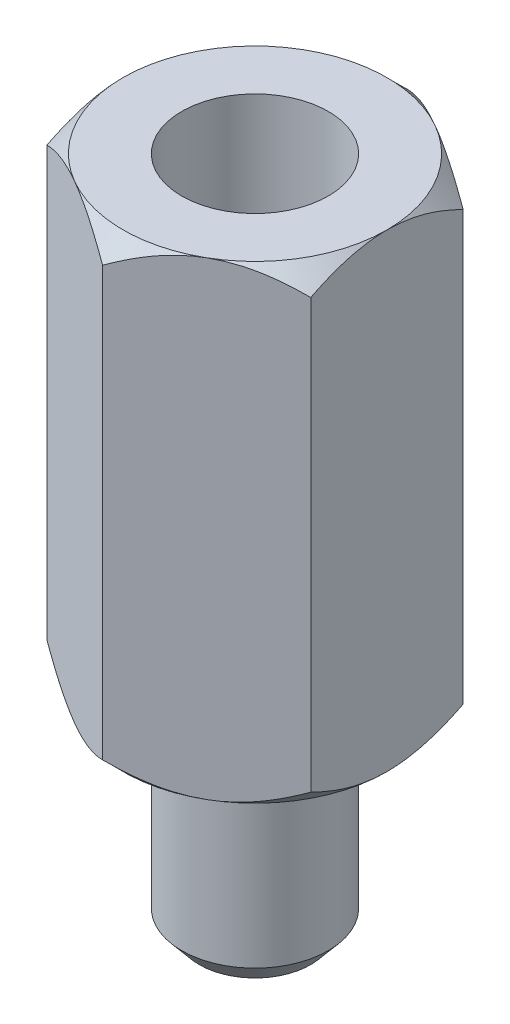
SolidWorks part; units mm, degrees
ref_plane "Front Plane" through (0, 0, 0) normal (0, 0, 1) x (1, 0, 0)
ref_plane "Top Plane" through (0, 0, 0) normal (0, 1, 0) x (1, 0, 0)
ref_plane "Right Plane" through (0, 0, 0) normal (1, 0, 0) x (0, 0, -1)
sketch "Sketch1" plane through (0, 0, 0) normal (0, 1, 0) x (1, 0, 0)
  circle A0 centre (0, 0) radius 1.25
  dimension "D1" = 2.5
extrude "Boss-Extrude1" add sketch "Sketch1" along normal blind 3.5
sketch "Sketch2" plane through (0, 3.5, 0) normal (0, 1, 0) x (1, 0, 0)
  line L1 (2.25, -1.299) -> (2.25, 1.299)
  line L2 (2.25, 1.299) -> (0, 2.5981)
  line L3 (0, 2.5981) -> (-2.25, 1.299)
  line L4 (-2.25, 1.299) -> (-2.25, -1.299)
  line L5 (-2.25, -1.299) -> (0, -2.5981)
  line L6 (0, -2.5981) -> (2.25, -1.299)
  circle A0 centre (0, 0) radius 2.25 construction
  point P1 (-1.6655, -0.9596)
  dimension "D1" = 4.5
extrude "Boss-Extrude2" add sketch "Sketch2" along normal blind 8
sketch "Sketch3" plane through (0, 11.5, 0) normal (0, 1, 0) x (1, 0, 0)
  circle A0 centre (0, 0) radius 1.25
  dimension "D1" = 2.5
extrude "Cut-Extrude1" cut sketch "Sketch3" against normal blind 4.8
sketch "Sketch5" plane through (0, 11.5, 0) normal (0, 1, 0) x (1, 0, 0)
  line L0 (0, 2.5981) -> (-2.25, 1.299) construction
  circle A0 centre (0, 0) radius 2.25
extrude "Cut-Extrude2" cut sketch "Sketch5" against normal through all draft 45 flip side to cut
sketch "Sketch6" plane through (0, 3.5, 0) normal (0, -1, 0) x (1, 0, 0)
  line L0 (-2.25, 1.299) -> (0, 2.5981) construction
  circle A0 centre (0, 0) radius 2.25
extrude "Cut-Extrude3" cut sketch "Sketch6" against normal through all draft 45 flip side to cut
chamfer "Chamfer1" distance 0.3 angle 50 1 edges at (0, 0, 1.25)
